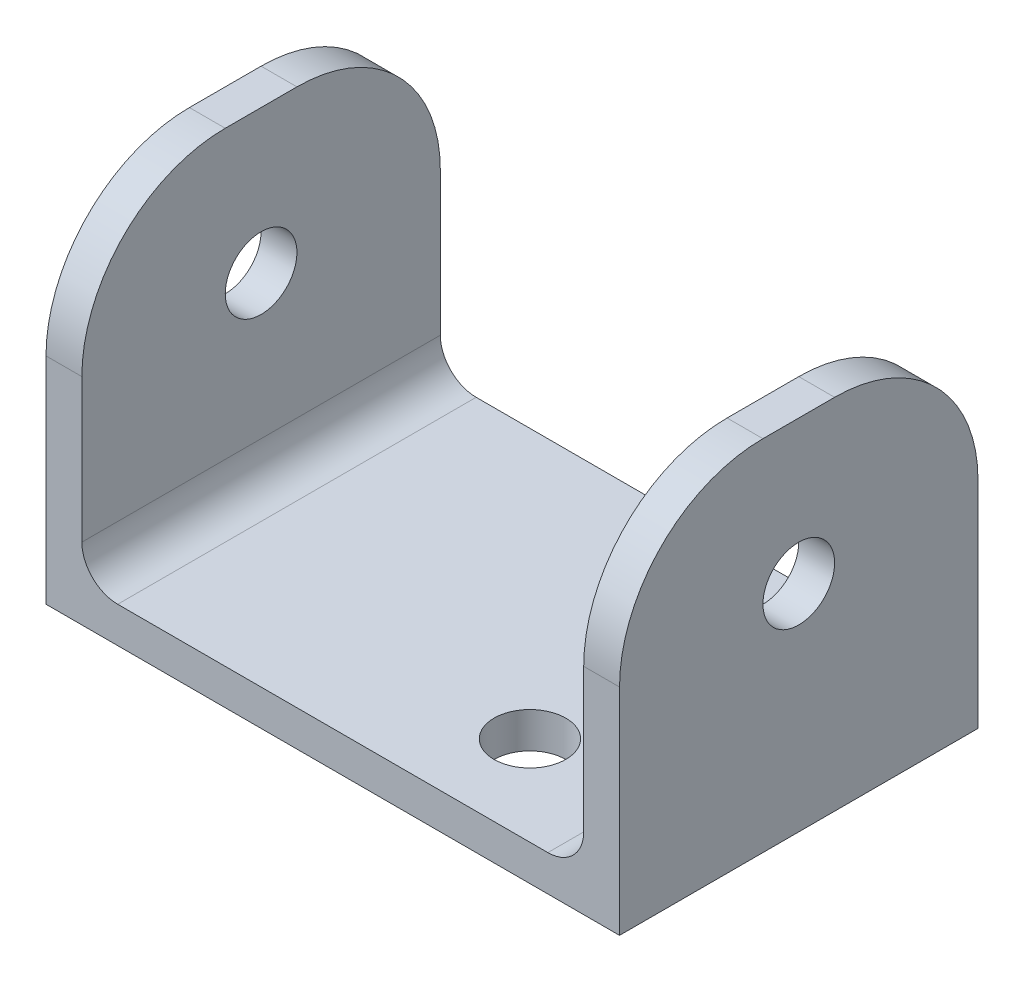
SolidWorks part; units mm, degrees
material "6061-T6 (SS)"
ref_plane "Front" through (0, 0, 0) normal (0, 0, 1) x (1, 0, 0)
ref_plane "Top" through (0, 0, 0) normal (0, 1, 0) x (1, 0, 0)
ref_plane "Right" through (0, 0, 0) normal (1, 0, 0) x (0, 0, -1)
sketch "Sketch1" plane through (0, 0, 0) normal (0, 0, 1) x (1, 0, 0)
  line L1 (-25.4, 15.875) -> (25.4, 15.875)
  line L2 (-25.4, 15.875) -> (-25.4, -15.875)
  line L3 (-25.4, -15.875) -> (25.4, -15.875)
  line L4 (25.4, 15.875) -> (25.4, -15.875)
  line L5 (-25.4, 15.875) -> (25.4, -15.875) construction
  line L6 (-25.4, -15.875) -> (25.4, 15.875) construction
  point P0 (0, 0)
  dimension "D1" = 31.75
  dimension "D2" = 50.8
extrude "Boss-Extrude1" add sketch "Sketch1" along normal mid plane 31.75
sketch "Sketch2" plane through (0, 0, 15.875) normal (0, 0, 1) x (1, 0, 0)
  line L0 (25.4, 15.875) -> (-25.4, 15.875) construction
  line L1 (-22.225, 15.875) -> (22.225, 15.875)
  line L2 (-22.225, 15.875) -> (-22.225, -12.7)
  line L3 (-22.225, -12.7) -> (22.225, -12.7)
  line L4 (22.225, 15.875) -> (22.225, -12.7)
  line L5 (0, 0) -> (0, 15.875) construction
  line L6 (25.4, -15.875) -> (25.4, 15.875) construction
  line L7 (-25.4, -15.875) -> (25.4, -15.875) construction
  dimension "D1" = 3.175
  dimension "D2" = 3.175
extrude "Cut-Extrude1" cut sketch "Sketch2" against normal through all
sketch "Sketch3" plane through (0, -12.7, 0) normal (0, 1, 0) x (1, 0, 0)
  line L0 (9.525, 7.9375) -> (9.525, -7.9375) construction
  line L3 (0, 0) -> (22.225, 0) construction
  line L4 (22.225, 15.875) -> (22.225, -15.875) construction
  circle A0 centre (9.525, 7.9375) radius 3.175
  circle A1 centre (9.525, -7.9375) radius 3.175
  point P4 (9.525, 0)
  dimension "D1" = 15.875
  dimension "D2" = 6.35
  dimension "D3" = 12.7
extrude "Cut-Extrude2" cut sketch "Sketch3" against normal through all
fillet "Fillet1" radius 3.175 2 edges at (-22.225, -12.7, 0) (22.225, -12.7, 0)
sketch "Sketch4" plane through (25.4, 0, 0) normal (1, 0, 0) x (0, 0, -1)
  line L0 (0, 15.875) -> (0, -15.875) construction
  line L4 (-15.875, 15.875) -> (15.875, 15.875) construction
  line L5 (-15.875, -15.875) -> (15.875, -15.875) construction
  circle A0 centre (0, 3.175) radius 3.175
  dimension "D1" = 19.05
  dimension "D2" = 6.35
extrude "Cut-Extrude3" cut sketch "Sketch4" against normal through all
fillet "Fillet2" radius 12.7 4 edges at (-23.8125, 15.875, 15.875) (-23.8125, 15.875, -15.875) (23.8125, 15.875, -15.875) (23.8125, 15.875, 15.875)
sketch3d "3DSketch1"
  line L0 (25.4, 3.175, 0) -> (-25.4, 3.175, 0) construction
  line L1 (22.225, 3.175, 0) -> (25.4, 3.175, 0) construction
  line L2 (-25.4, 3.175, 0) -> (-22.225, 3.175, 0) construction
  circle A0 centre (-22.225, 3.175, 0) radius 3.175 construction
  point P6 (-9.525, 3.175, 0)
  point P9 (-25.4, 3.175, 0)
  dimension "D1" = 12.7
